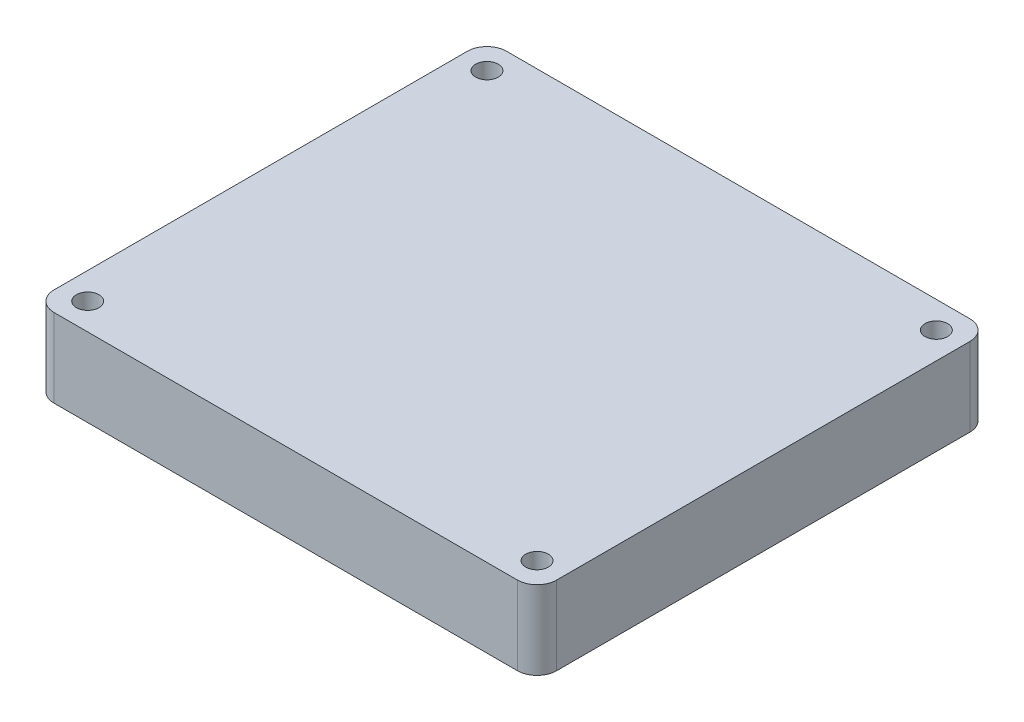
SolidWorks part; units mm, degrees
ref_plane "Front Plane" through (0, 0, 0) normal (0, 0, 1) x (1, 0, 0)
ref_plane "Top Plane" through (0, 0, 0) normal (0, 1, 0) x (1, 0, 0)
ref_plane "Right Plane" through (0, 0, 0) normal (1, 0, 0) x (0, 0, -1)
sketch "Sketch1" plane through (0, 0, 0) normal (0, 1, 0) x (1, 0, 0)
  line L1 (-66.0265, -6.8851) -> (-1.0279, -6.8851)
  line L2 (-66.0265, -6.8851) -> (-66.0265, 51.6365)
  line L3 (-66.0265, 51.6365) -> (-1.0279, 51.6365)
  line L4 (-1.0279, -6.8851) -> (-1.0279, 51.6365)
  dimension "D1" = 64.9986
  dimension "D2" = 58.5216
extrude "Boss-Extrude1" add sketch "Sketch1" along normal blind 10.16
sketch "Sketch2" plane through (0, 10.16, 0) normal (0, 1, 0) x (1, 0, 0)
  line L0 (-66.0265, -6.8851) -> (-1.0279, -6.8851) construction
  line L1 (-1.0279, -6.8851) -> (-1.0279, 51.6365) construction
  line L2 (-33.5272, 51.6365) -> (-33.5272, -6.8851) construction
  line L3 (-1.0279, 51.6365) -> (-66.0265, 51.6365) construction
  line L4 (-66.0265, 22.3757) -> (-1.0279, 22.3757) construction
  line L5 (-66.0265, 51.6365) -> (-66.0265, -6.8851) construction
  circle A0 centre (-4.4696, -3.4434) radius 1.4605
  circle A1 centre (-4.4696, 48.1948) radius 1.4605
  circle A2 centre (-62.5848, 48.1948) radius 1.4605
  circle A3 centre (-62.5848, -3.4434) radius 1.4605
  dimension "D1" = 3.4417
  dimension "D2" = 3.4417
extrude "Cut-Extrude1" cut sketch "Sketch2" against normal blind 10.16
fillet "Fillet1" radius 2.54 4 edges at (-1.0279, 5.08, 6.8851) (-1.0279, 5.08, -51.6365) (-66.0265, 5.08, 6.8851) (-66.0265, 5.08, -51.6365)
sketch "Sketch3" plane through (0, 0, 0) normal (0, -1, 0) x (1, 0, 0)
  line L0 (-33.5272, 6.8851) -> (-33.5272, -51.6365) construction
  line L1 (-63.4865, 6.8851) -> (-3.5679, 6.8851) construction
  line L2 (-3.5679, -51.6365) -> (-63.4865, -51.6365) construction
